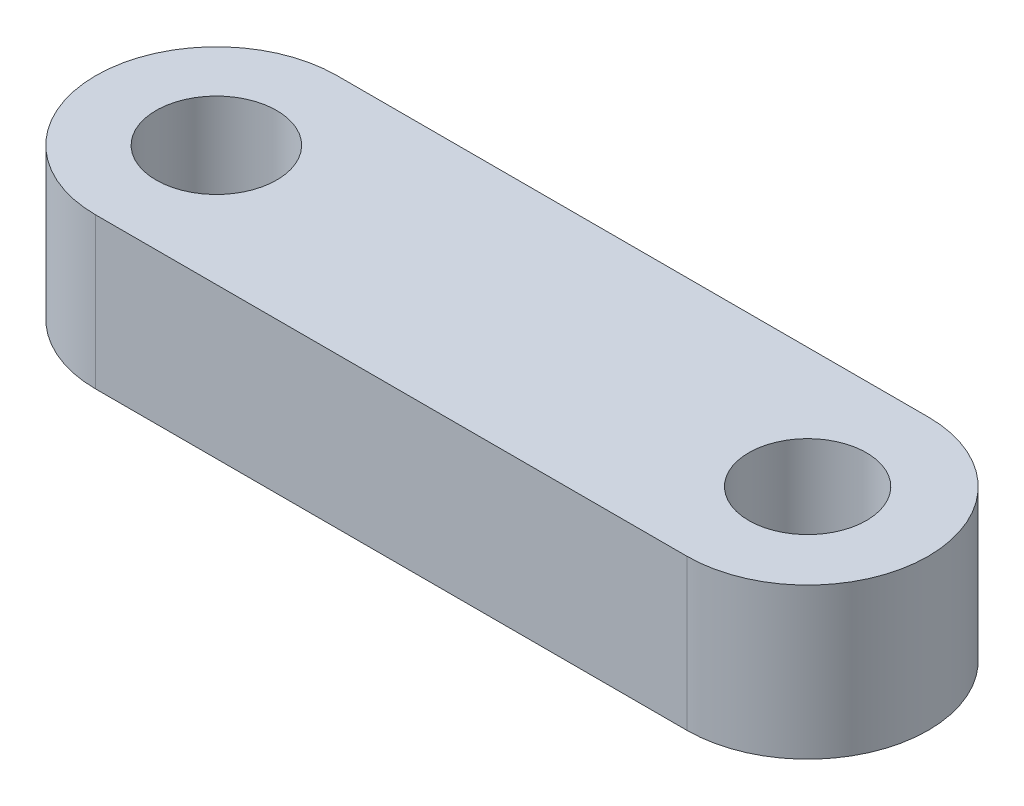
SolidWorks part; units mm, degrees
ref_plane "前视基准面" through (0, 0, 0) normal (0, 0, 1) x (1, 0, 0)
ref_plane "上视基准面" through (0, 0, 0) normal (0, 1, 0) x (1, 0, 0)
ref_plane "右视基准面" through (0, 0, 0) normal (1, 0, 0) x (0, 0, -1)
sketch "草图1" plane through (0, 0, 0) normal (0, 1, 0) x (1, 0, 0)
  line L0 (0, 0) -> (19.604, 0) construction
  line L1 (0, 4) -> (19.604, 4)
  line L2 (0, -4) -> (19.604, -4)
  arc A0 (0, 4) -> (0, -4) centre (0, 0) ccw
  arc A1 (19.604, -4) -> (19.604, 4) centre (19.604, 0) ccw
  circle A2 centre (0, 0) radius 2
  circle A3 centre (19.604, 0) radius 1.95
  point P3 (9.802, 0)
  dimension "D1" = 19.604
  dimension "D2" = 4
  dimension "D3" = 3.9
  dimension "D4" = 4
extrude "凸台-拉伸1" add sketch "草图1" along normal blind 5
